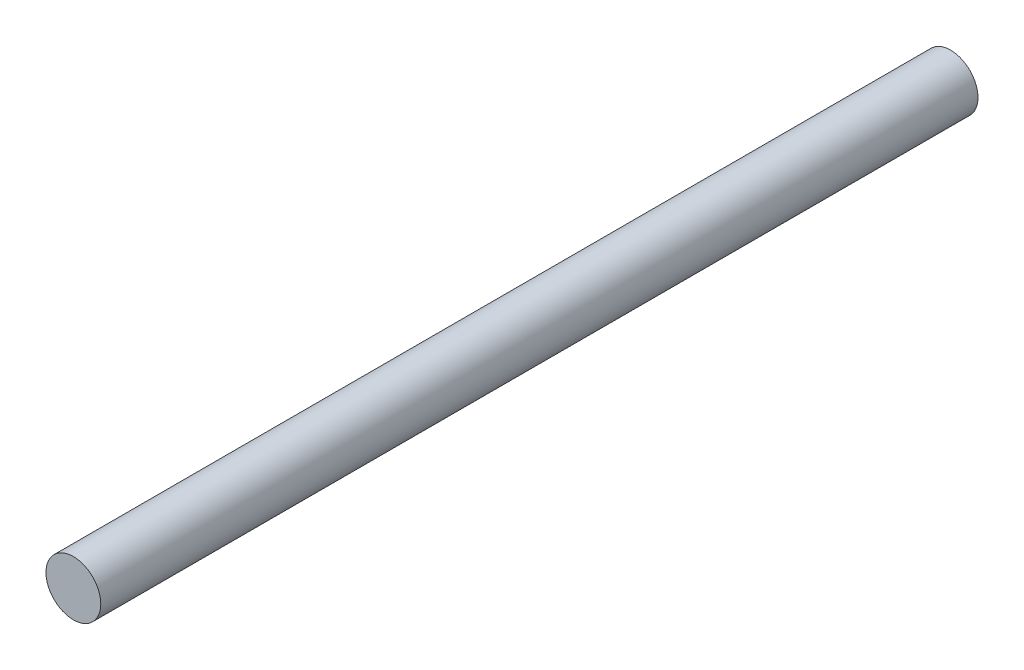
SolidWorks part; units mm, degrees
ref_plane "Front Plane" through (0, 0, 0) normal (0, 0, 1) x (1, 0, 0)
ref_plane "Top Plane" through (0, 0, 0) normal (0, 1, 0) x (1, 0, 0)
ref_plane "Right Plane" through (0, 0, 0) normal (1, 0, 0) x (0, 0, -1)
sketch "Sketch1" plane through (0, 0, 0) normal (0, 0, 1) x (1, 0, 0)
  circle A0 centre (0, 0) radius 2.5
  dimension "D1" = 5
extrude "Boss-Extrude1" add sketch "Sketch1" along normal blind 80
